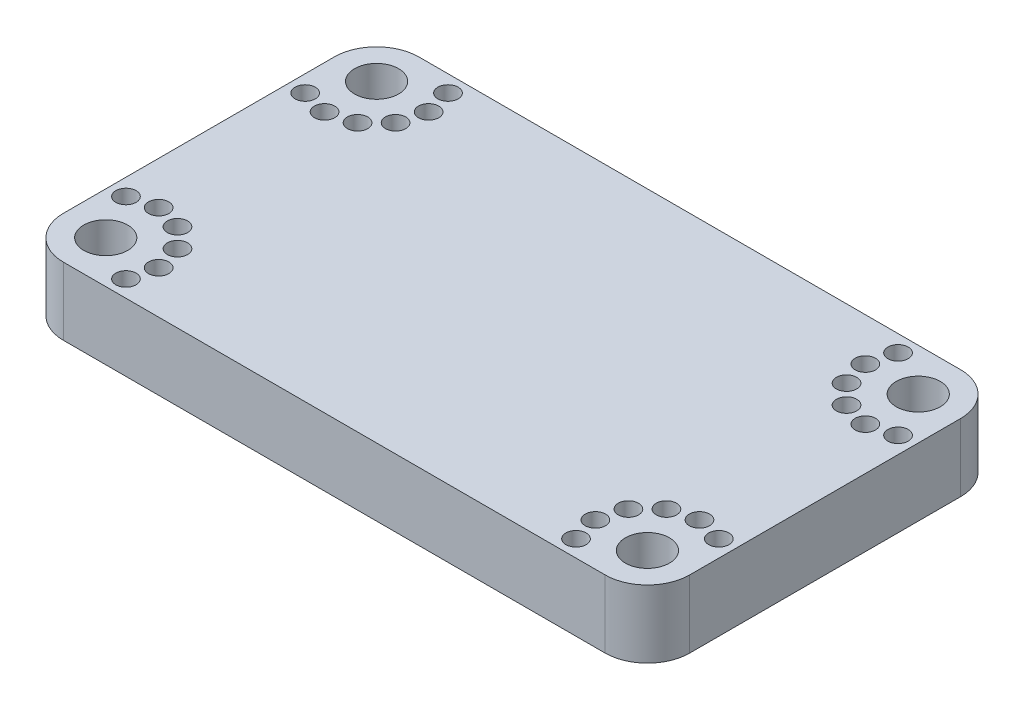
SolidWorks part; units mm, degrees
ref_plane "Front Plane" through (0, 0, 0) normal (0, 0, 1) x (1, 0, 0)
ref_plane "Top Plane" through (0, 0, 0) normal (0, 1, 0) x (1, 0, 0)
ref_plane "Right Plane" through (0, 0, 0) normal (1, 0, 0) x (0, 0, -1)
sketch "Sketch1" plane through (0, 0, 0) normal (0, 1, 0) x (1, 0, 0)
  line L1 (-40, -26.25) -> (40, -26.25)
  line L2 (-46.25, -20) -> (-46.25, 20)
  line L3 (-40, 26.25) -> (40, 26.25)
  line L4 (46.25, -20) -> (46.25, 20)
  line L5 (-46.25, -26.25) -> (46.25, 26.25) construction
  line L6 (-46.25, 26.25) -> (46.25, -26.25) construction
  arc A0 (-40, -26.25) -> (-46.25, -20) centre (-40, -20) cw
  arc A1 (40, -26.25) -> (46.25, -20) centre (40, -20) ccw
  arc A2 (40, 26.25) -> (46.25, 20) centre (40, 20) cw
  arc A3 (-46.25, 20) -> (-40, 26.25) centre (-40, 20) cw
  circle A4 centre (-40, 20) radius 3.25
  circle A5 centre (-40, -20) radius 3.25
  circle A6 centre (40, -20) radius 3.25
  circle A7 centre (40, 20) radius 3.25
  circle A8 centre (-43.7804, 13.2346) radius 1.5
  circle A9 centre (-39.9347, 12.2503) radius 1.5
  circle A10 centre (-40, 20) radius 7.75 construction
  circle A11 centre (-43.7804, 13.2346) radius 2.4696 construction
  circle A12 centre (-39.9347, 12.2503) radius 2.4696 construction
  circle A13 centre (-36.1062, 13.2992) radius 2.4696 construction
  circle A14 centre (-36.1062, 13.2992) radius 1.5
  circle A15 centre (-33.2992, 16.1062) radius 2.4696 construction
  circle A16 centre (-33.2992, 16.1062) radius 1.5
  circle A17 centre (-32.2503, 19.9347) radius 2.4696 construction
  circle A18 centre (-32.2503, 19.9347) radius 1.5
  circle A19 centre (-33.2346, 23.7804) radius 2.4696 construction
  circle A20 centre (-33.2346, 23.7804) radius 1.5
  circle A21 centre (-40, -20) radius 7.75 construction
  circle A22 centre (40, -20) radius 7.75 construction
  circle A23 centre (40, 20) radius 7.75 construction
  circle A24 centre (-33.2346, -23.7804) radius 1.5
  circle A25 centre (-32.2503, -19.9347) radius 1.5
  circle A26 centre (-33.2992, -16.1062) radius 1.5
  circle A27 centre (-36.1062, -13.2992) radius 1.5
  circle A28 centre (-39.9347, -12.2503) radius 1.5
  circle A29 centre (-43.7804, -13.2346) radius 1.5
  circle A30 centre (33.2346, 23.7804) radius 1.5
  circle A31 centre (32.2503, 19.9347) radius 1.5
  circle A32 centre (33.2992, 16.1062) radius 1.5
  circle A34 centre (39.9347, 12.2503) radius 1.5
  circle A35 centre (43.7804, 13.2346) radius 1.5
  circle A36 centre (36.1062, 13.2992) radius 1.5
  circle A37 centre (33.2346, -23.7804) radius 1.5
  circle A38 centre (32.2503, -19.9347) radius 1.5
  circle A39 centre (33.2992, -16.1062) radius 1.5
  circle A40 centre (36.1062, -13.2992) radius 1.5
  circle A41 centre (39.9347, -12.2503) radius 1.5
  circle A42 centre (43.7804, -13.2346) radius 1.5
  point P0 (0, 0)
  dimension "D1" = 3
  dimension "D2" = 6.5
  dimension "D3" = 3
  dimension "D4" = 0.9696
  dimension "D5" = 80
  dimension "D6" = 40
extrude "Boss-Extrude1" add sketch "Sketch1" along normal blind 10
sketch "Sketch2" plane through (0, 0, -26.25) normal (0, 0, -1) x (-1, 0, 0)
  line L0 (0, 10) -> (0, 7.2045)
  line L1 (-40, 10) -> (40, 10) construction
  line L2 (-2.6628, 7.2045) -> (2.6628, 7.2045)
  line L3 (2.6628, 7.2045) -> (7.9883, 7.2045)
  line L4 (-2.6628, 7.2045) -> (-7.9883, 7.2045)
  circle A0 centre (-7.9883, 7.2045) radius 1.6629
  circle A1 centre (-2.6628, 7.2045) radius 1.6629
  circle A2 centre (2.6628, 7.2045) radius 1.6629
  circle A3 centre (7.9883, 7.2045) radius 1.6629
